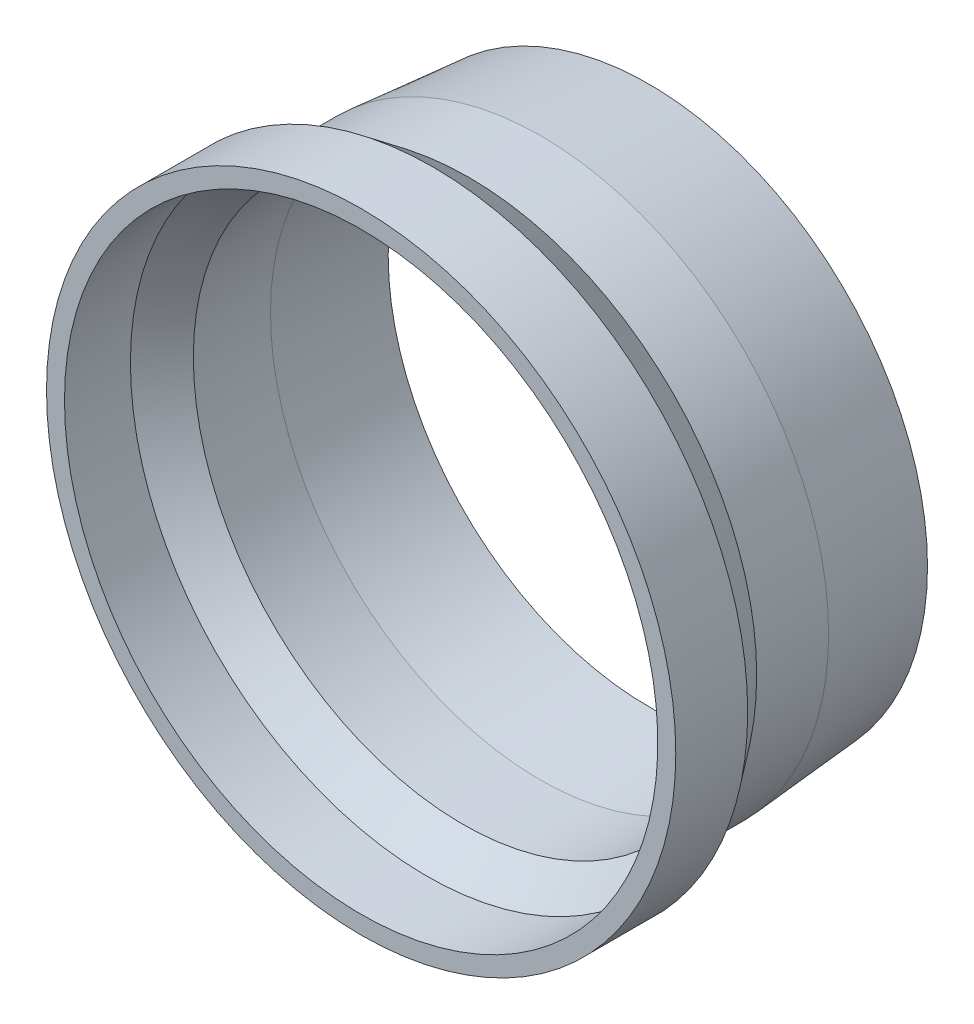
SolidWorks part; units mm, degrees
ref_plane "Front Plane" through (0, 0, 0) normal (0, 0, 1) x (1, 0, 0)
ref_plane "Top Plane" through (0, 0, 0) normal (0, 1, 0) x (1, 0, 0)
ref_plane "Right Plane" through (0, 0, 0) normal (1, 0, 0) x (0, 0, -1)
sketch "Sketch1" plane through (0, 0, 0) normal (1, 0, 0) x (0, 0, -1)
  line L0 (0, 0) -> (-126.0707, 0) construction
  line L1 (-39.1583, 52.3875) -> (-32.8083, 47.625)
  line L3 (-31.75, 50.8) -> (-38.1, 55.5625)
  line L5 (-38.1, 55.5625) -> (-50.8, 55.5625)
  line L6 (-50.8, 55.5625) -> (-50.8, 52.3875)
  line L7 (-50.8, 52.3875) -> (-39.1583, 52.3875)
  line L8 (-31.75, 50.8) -> (-19.05, 50.8)
  line L9 (-19.05, 50.8) -> (0, 49.2125)
  line L10 (0, 49.2125) -> (0, 46.0265)
  line L11 (0, 46.0265) -> (-19.1821, 47.625)
  line L12 (-19.1821, 47.625) -> (-32.8083, 47.625)
  point P13 (0, 47.6195)
  dimension "D1" = 3.175
  dimension "D2" = 3.175
  dimension "D3" = 104.775
  dimension "D4" = 101.6
  dimension "D5" = 3.175
  dimension "D6" = 12.7
  dimension "D7" = 98.425
  dimension "D8" = 3.175
  dimension "D9" = 12.7
  dimension "D10" = 19.05
  dimension "D11" = 6.35
revolve "Revolve1" add sketch "Sketch1" angle 360 about L0
